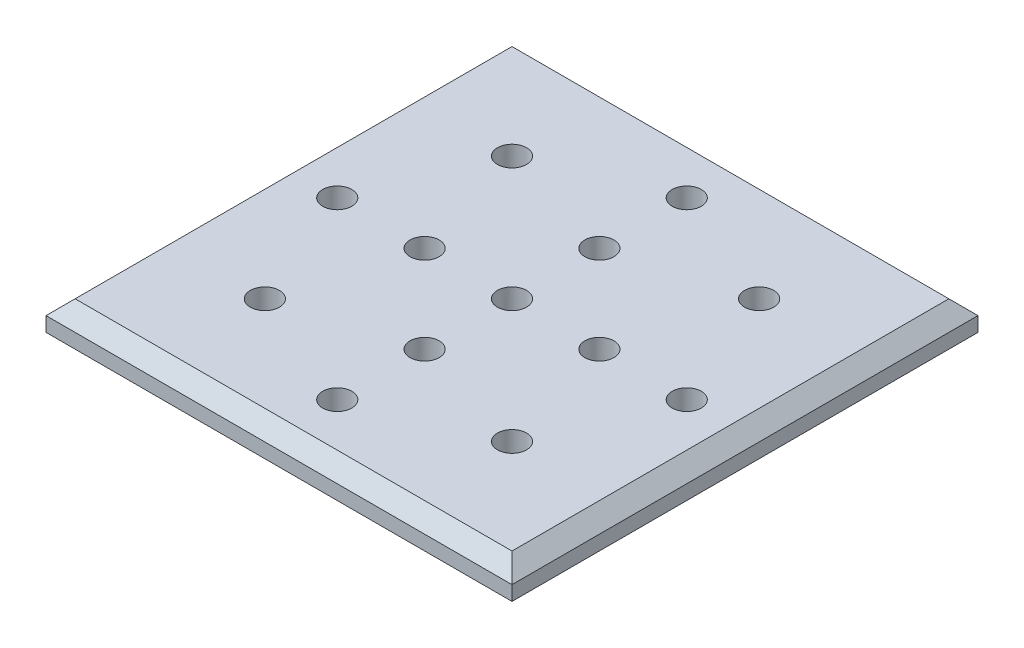
SolidWorks part; units mm, degrees
material "Al - 6061 Polished"
ref_plane "Front Plane" through (0, 0, 0) normal (0, 0, 1) x (1, 0, 0)
ref_plane "Top Plane" through (0, 0, 0) normal (0, 1, 0) x (1, 0, 0)
ref_plane "Right Plane" through (0, 0, 0) normal (1, 0, 0) x (0, 0, -1)
sketch "Sketch1" plane through (0, 0, 0) normal (0, 1, 0) x (1, 0, 0)
  line L2 (-50.8, -50.8) -> (50.8, -50.8)
  line L3 (-50.8, -50.8) -> (-50.8, 50.8)
  line L4 (-50.8, 50.8) -> (50.8, 50.8)
  line L5 (50.8, -50.8) -> (50.8, 50.8)
  line L6 (-50.8, -50.8) -> (50.8, 50.8) construction
  line L7 (-50.8, 50.8) -> (50.8, -50.8) construction
  point P2 (0, 0)
  dimension "D1" = 101.6
extrude "Boss-Extrude1" add sketch "Sketch1" along normal blind 9.525
sketch "Sketch2" plane through (0, 0, 0) normal (0, -1, 0) x (1, 0, 0)
  line L0 (47.498, 47.498) -> (-47.498, 47.498)
  line L1 (-47.498, 47.498) -> (-47.498, -47.498)
  line L2 (-47.498, -47.498) -> (47.498, -47.498)
  line L3 (47.498, -47.498) -> (47.498, 47.498)
  line L4 (50.8, -50.8) -> (50.8, 50.8)
  line L5 (50.8, 50.8) -> (-50.8, 50.8)
  line L6 (-50.8, 50.8) -> (-50.8, -50.8)
  line L7 (-50.8, -50.8) -> (50.8, -50.8)
  line L8 (50.8, -50.8) -> (50.8, 50.8)
  line L9 (50.8, 50.8) -> (-50.8, 50.8)
  line L10 (-50.8, 50.8) -> (-50.8, -50.8)
  line L11 (-50.8, -50.8) -> (50.8, -50.8)
  dimension "D1" = 0
  dimension "D2" = 3.302
extrude "Cut-Extrude1" cut sketch "Sketch2" against normal blind 3.175
chamfer "Chamfer1" distance 3.175 angle 45 4 edges at (0, 9.525, 50.8) (-50.8, 9.525, 0) (0, 9.525, -50.8) (50.8, 9.525, 0)
sketch "Sketch3" [suppressed] plane through (0, 9.525, 0) normal (0, 1, 0) x (1, 0, 0)
  line L0 (50.8, 50.8) -> (38.1, -38.1) construction
  line L1 (38.1, -38.1) -> (50.8, 50.8) construction
  line L2 (50.8, 50.8) -> (-38.1, 38.1) construction
  line L3 (38.1, 38.1) -> (38.1, -38.1) construction
  line L4 (38.1, 38.1) -> (38.1, -38.1) construction
  line L5 (38.1, -38.1) -> (114.3, -38.1) construction
  line L6 (38.1, -38.1) -> (38.1, 38.1) construction
  line L7 (38.1, -38.1) -> (21.1439, 36.1895) construction
  line L8 (-38.1, 38.1) -> (-38.1, -38.1) construction
  line L9 (-38.1, 38.1) -> (-21.1439, -36.1895) construction
  circle A0 centre (38.1, -38.1) radius 76.2 construction
  circle A3 centre (38.1, 38.1) radius 3.175 construction
  circle A4 centre (-38.1, 38.1) radius 76.2 construction
  circle A5 centre (21.1439, 36.1895) radius 3.175
  circle A6 centre (5.0381, 30.5538) radius 3.175
  circle A7 centre (-9.4099, 21.4756) radius 3.175
  circle A8 centre (-21.4756, 9.4099) radius 3.175
  circle A9 centre (-30.5538, -5.0381) radius 3.175
  circle A10 centre (-36.1895, -21.1439) radius 3.175
  circle A11 centre (-38.1, -38.1) radius 3.175
  circle A12 centre (-21.1439, -36.1895) radius 3.175
  circle A13 centre (-5.0381, -30.5538) radius 3.175
  circle A14 centre (9.4099, -21.4756) radius 3.175
  circle A15 centre (21.4756, -9.4099) radius 3.175
  circle A16 centre (30.5538, 5.0381) radius 3.175
  circle A17 centre (36.1895, 21.1439) radius 3.175
  circle A18 centre (38.1, 38.1) radius 3.175
  dimension "D5" = 152.4
  dimension "D6" = 6.35
  dimension "D1" = 88.9
  dimension "D2" = 12.7
  dimension "D3" = 88.9
  dimension "D4" = 12.7
  dimension "D7" = 90
  dimension "D9" = 12.857
  dimension "D11" = 12.857
  dimension "D8" = 8
  dimension "D10" = 8
extrude "Diana Hole Pattern" [suppressed] cut sketch "Sketch3" against normal through all
sketch "Sketch9" plane through (0, 0, 0) normal (0, 1, 0) x (1, 0, 0)
  circle A0 centre (0, 0) radius 3.175
  circle A11 centre (19.05, 0) radius 3.175
  circle A12 centre (0, -19.05) radius 3.175
  circle A13 centre (-19.05, 0) radius 3.175
  circle A14 centre (0, 19.05) radius 3.175
  circle A16 centre (38.1, 0) radius 3.175
  circle A17 centre (26.9408, -26.9408) radius 3.175
  circle A18 centre (0, -38.1) radius 3.175
  circle A19 centre (-26.9408, -26.9408) radius 3.175
  circle A20 centre (-38.1, 0) radius 3.175
  circle A21 centre (-26.9408, 26.9408) radius 3.175
  circle A22 centre (0, 38.1) radius 3.175
  circle A23 centre (26.9408, 26.9408) radius 3.175
  point P14 (0, 0)
  point P15 (0, 0)
  dimension "D1" = 6.35
  dimension "D3" = 4
  dimension "D2" = 19.05
  dimension "D4" = 38.1
  dimension "D5" = 8
sketch "Sketch10" plane through (0, 0, 0) normal (0, -1, 0) x (1, 0, 0)
extrude "Cut-Extrude3" cut sketch "Sketch9" along normal blind 55.118
